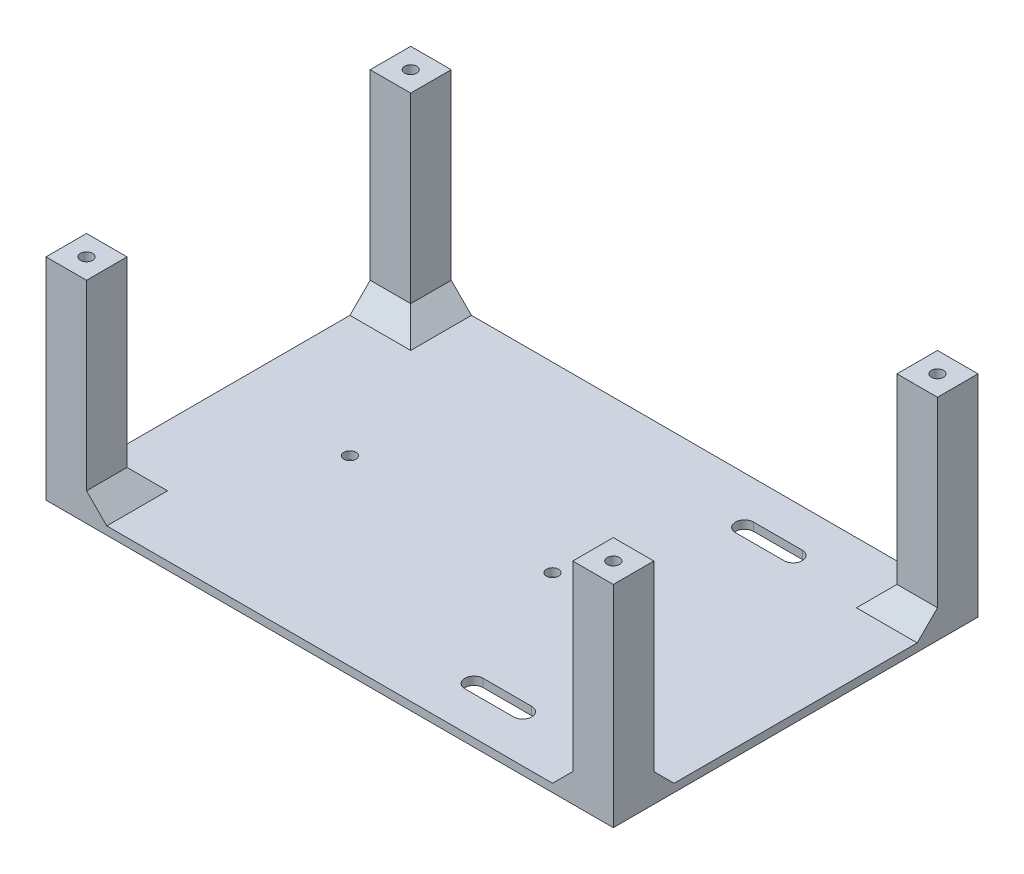
SolidWorks part; units mm, degrees
ref_plane "Front Plane" through (0, 0, 0) normal (0, 0, 1) x (1, 0, 0)
ref_plane "Top Plane" through (0, 0, 0) normal (0, 1, 0) x (1, 0, 0)
ref_plane "Right Plane" through (0, 0, 0) normal (1, 0, 0) x (0, 0, -1)
sketch "Sketch1" plane through (0, 0, 0) normal (0, 1, 0) x (1, 0, 0)
  line L1 (70, -45) -> (-70, -45)
  line L2 (70, -45) -> (70, 45)
  line L3 (70, 45) -> (-70, 45)
  line L4 (-70, -45) -> (-70, 45)
  line L5 (70, -45) -> (-70, 45) construction
  line L6 (70, 45) -> (-70, -45) construction
  point P0 (0, 0)
  dimension "D1" = 140
  dimension "D2" = 90
extrude "Boss-Extrude1" add sketch "Sketch1" along normal blind 2
sketch "Sketch2" plane through (0, 2, 0) normal (0, 1, 0) x (1, 0, 0)
  line L1 (-70, 45) -> (-60, 45)
  line L2 (-70, 45) -> (-70, 35)
  line L3 (-70, 35) -> (-60, 35)
  line L4 (-60, 45) -> (-60, 35)
  line L5 (70, 45) -> (60, 45)
  line L6 (70, 45) -> (70, 35)
  line L7 (70, 35) -> (60, 35)
  line L8 (60, 45) -> (60, 35)
  line L9 (70, -45) -> (60, -45)
  line L10 (70, -45) -> (70, -35)
  line L11 (70, -35) -> (60, -35)
  line L12 (60, -45) -> (60, -35)
  line L13 (-70, -45) -> (-60, -45)
  line L14 (-70, -45) -> (-70, -35)
  line L15 (-70, -35) -> (-60, -35)
  line L16 (-60, -45) -> (-60, -35)
  dimension "D1" = 10
extrude "Boss-Extrude2" add sketch "Sketch2" along normal blind 50
chamfer "Chamfer1" distance 5 angle 45 8 edges at (65, 2, 35) (60, 2, 40) (65, 2, -35) (60, 2, -40) (-60, 2, 40) (-65, 2, 35) (-60, 2, -40) (-65, 2, -35)
sketch "Sketch3" plane through (0, 52, 0) normal (0, 1, 0) x (1, 0, 0)
  line L0 (-70, 45) -> (-60, 35) construction
  line L1 (70, 45) -> (60, 35) construction
  line L2 (70, -45) -> (60, -35) construction
  line L3 (-70, -45) -> (-60, -35) construction
  circle A0 centre (-65, 40) radius 1.5
  circle A1 centre (65, 40) radius 1.5
  circle A2 centre (65, -40) radius 1.5
  circle A3 centre (-65, -40) radius 1.5
  dimension "D1" = 3
extrude "Cut-Extrude1" cut sketch "Sketch3" against normal through all
sketch "Sketch4" plane through (0, 2, 0) normal (0, 1, 0) x (1, 0, 0)
  line L3 (-70, 30) -> (-70, -30) construction
  circle A0 centre (-40, 0) radius 1.5
  circle A1 centre (10, 0) radius 1.5
  point P4 (0, 0)
  point P5 (0, 0)
  point P6 (0, 0)
  point P7 (0, 0)
  point P8 (0, 0)
  point P9 (0, 0)
  point P10 (0, 0)
  point P11 (0, 0)
  point P12 (0, 0)
  point P13 (-10, 32.6)
  point P14 (32.9333, 6.9733)
  point P15 (0, 0)
  point P16 (0, 0)
  point P17 (-35.3574, -29.3493)
  point P18 (0, 0)
  point P20 (0, 0)
  point P23 (0, 0)
  point P24 (0, 0)
  dimension "D2" = 3
  dimension "D1" = 50
  dimension "D4" = 30
extrude "Cut-Extrude2" cut sketch "Sketch4" against normal through all
sketch "Sketch5" plane through (0, 2, 0) normal (0, 1, 0) x (1, 0, 0)
  line L0 (24, 33.38) -> (36, 33.38) construction
  line L1 (24, 35.63) -> (36, 35.63)
  line L2 (24, 31.13) -> (36, 31.13)
  arc A0 (24, 35.63) -> (24, 31.13) centre (24, 33.38) ccw
  arc A1 (36, 31.13) -> (36, 35.63) centre (36, 33.38) ccw
  point P2 (30, 33.38)
  point P7 (22.9159, 31.13)
  dimension "D1" = 12
  dimension "D2" = 4.5
  dimension "D3" = 33.38
  dimension "D4" = 30
extrude "Cut-Extrude3" cut sketch "Sketch5" against normal through all
mirror "Mirror1" about plane through (0, 0, 0) normal (0, 0, 1) of "Cut-Extrude3"
